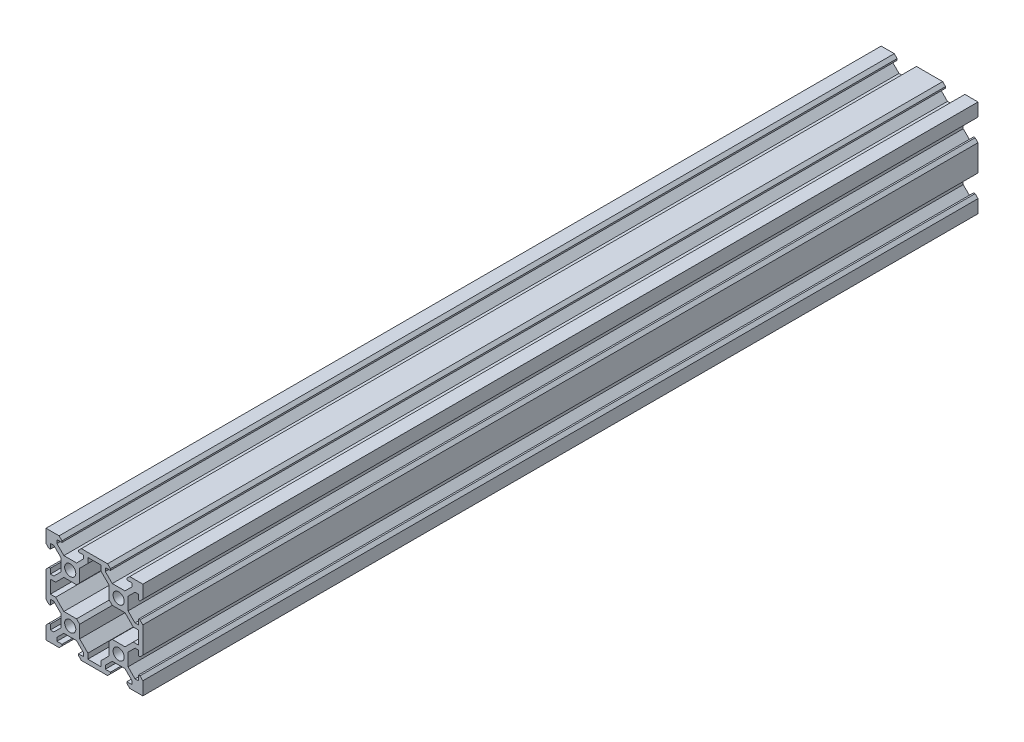
SolidWorks part; units mm, degrees
ref_plane "Front Plane" through (0, 0, 0) normal (0, 0, 1) x (1, 0, 0)
ref_plane "Top Plane" through (0, 0, 0) normal (0, 1, 0) x (1, 0, 0)
ref_plane "Right Plane" through (0, 0, 0) normal (1, 0, 0) x (0, 0, -1)
sketch "Sketch1" plane through (0, 0, 0) normal (0, 0, 1) x (1, 0, 0)
  line L1 (0, 0) -> (40, 0)
  line L2 (0, 0) -> (0, 40)
  line L3 (0, 40) -> (40, 40)
  line L4 (40, 0) -> (40, 40)
  dimension "D1" = 40
extrude "Boss-Extrude1" add sketch "Sketch1" against normal blind 345
sketch "Sketch2" plane through (0, 0, 0) normal (0, 0, 1) x (1, 0, 0)
  line L0 (0, 20) -> (40, 20) construction
  line L1 (0, 40) -> (0, 0) construction
  line L2 (40, 0) -> (40, 40) construction
  line L3 (20, 40) -> (20, 0) construction
  line L4 (40, 40) -> (0, 40) construction
  line L5 (0, 0) -> (40, 0) construction
  line L6 (6.605, 38.815) -> (6.605, 38.2)
  line L7 (6.605, 38.2) -> (4.5, 38.2)
  line L8 (4.5, 38.2) -> (4.5, 36.7728)
  line L9 (4.5, 36.7728) -> (7.3728, 33.9)
  line L10 (7.3728, 33.9) -> (12.6272, 33.9)
  line L11 (12.6272, 33.9) -> (15.5, 36.7728)
  line L12 (15.5, 36.7728) -> (15.5, 38.2)
  line L13 (15.5, 38.2) -> (13.395, 38.2)
  line L14 (13.395, 38.2) -> (13.395, 38.815)
  line L16 (6.605, 38.815) -> (5.42, 40)
  line L17 (13.395, 38.815) -> (14.58, 40)
  line L18 (14.58, 40) -> (5.42, 40)
  line L19 (26.605, 38.815) -> (25.42, 40)
  line L20 (26.605, 38.2) -> (26.605, 38.815)
  line L21 (24.5, 38.2) -> (26.605, 38.2)
  line L22 (24.5, 36.7728) -> (24.5, 38.2)
  line L23 (27.3728, 33.9) -> (24.5, 36.7728)
  line L24 (32.6272, 33.9) -> (27.3728, 33.9)
  line L25 (35.5, 36.7728) -> (32.6272, 33.9)
  line L26 (35.5, 38.2) -> (35.5, 36.7728)
  line L27 (33.395, 38.2) -> (35.5, 38.2)
  line L28 (33.395, 38.815) -> (33.395, 38.2)
  line L29 (33.395, 38.815) -> (34.58, 40)
  line L30 (25.42, 40) -> (34.58, 40)
  line L31 (26.605, 1.8) -> (26.605, 1.185)
  line L32 (24.5, 1.8) -> (26.605, 1.8)
  line L33 (24.5, 3.2272) -> (24.5, 1.8)
  line L34 (27.3728, 6.1) -> (24.5, 3.2272)
  line L35 (32.6272, 6.1) -> (27.3728, 6.1)
  line L36 (35.5, 3.2272) -> (32.6272, 6.1)
  line L37 (35.5, 1.8) -> (35.5, 3.2272)
  line L38 (33.395, 1.8) -> (35.5, 1.8)
  line L39 (33.395, 1.185) -> (33.395, 1.8)
  line L40 (33.395, 1.185) -> (34.58, 0)
  line L41 (25.42, 0) -> (34.58, 0)
  line L42 (26.605, 1.185) -> (25.42, 0)
  line L43 (13.395, 1.185) -> (14.58, 0)
  line L44 (13.395, 1.8) -> (13.395, 1.185)
  line L45 (15.5, 1.8) -> (13.395, 1.8)
  line L46 (15.5, 3.2272) -> (15.5, 1.8)
  line L47 (12.6272, 6.1) -> (15.5, 3.2272)
  line L48 (7.3728, 6.1) -> (12.6272, 6.1)
  line L49 (4.5, 3.2272) -> (7.3728, 6.1)
  line L50 (4.5, 1.8) -> (4.5, 3.2272)
  line L51 (6.605, 1.8) -> (4.5, 1.8)
  line L52 (6.605, 1.185) -> (6.605, 1.8)
  line L53 (6.605, 1.185) -> (5.42, 0)
  line L54 (14.58, 0) -> (5.42, 0)
  line L55 (0, 0) -> (40, 40) construction
  line L56 (1.8, 13.395) -> (1.185, 13.395)
  line L57 (1.8, 15.5) -> (1.8, 13.395)
  line L58 (3.2272, 15.5) -> (1.8, 15.5)
  line L59 (6.1, 12.6272) -> (3.2272, 15.5)
  line L60 (6.1, 7.3728) -> (6.1, 12.6272)
  line L61 (3.2272, 4.5) -> (6.1, 7.3728)
  line L62 (1.8, 4.5) -> (3.2272, 4.5)
  line L63 (1.8, 6.605) -> (1.8, 4.5)
  line L64 (1.185, 6.605) -> (1.8, 6.605)
  line L65 (1.185, 6.605) -> (0, 5.42)
  line L66 (0, 14.58) -> (0, 5.42)
  line L67 (1.185, 13.395) -> (0, 14.58)
  line L68 (0, 40) -> (40, 0) construction
  line L69 (1.185, 26.605) -> (0, 25.42)
  line L70 (1.8, 26.605) -> (1.185, 26.605)
  line L71 (1.8, 24.5) -> (1.8, 26.605)
  line L72 (3.2272, 24.5) -> (1.8, 24.5)
  line L73 (6.1, 27.3728) -> (3.2272, 24.5)
  line L74 (6.1, 32.6272) -> (6.1, 27.3728)
  line L75 (3.2272, 35.5) -> (6.1, 32.6272)
  line L76 (1.8, 35.5) -> (3.2272, 35.5)
  line L77 (1.8, 33.395) -> (1.8, 35.5)
  line L78 (1.185, 33.395) -> (1.8, 33.395)
  line L79 (1.185, 33.395) -> (0, 34.58)
  line L80 (0, 25.42) -> (0, 34.58)
  line L81 (38.2, 15.5) -> (38.2, 13.395)
  line L82 (36.7728, 15.5) -> (38.2, 15.5)
  line L83 (33.9, 12.6272) -> (36.7728, 15.5)
  line L84 (33.9, 7.3728) -> (33.9, 12.6272)
  line L85 (36.7728, 4.5) -> (33.9, 7.3728)
  line L86 (38.2, 4.5) -> (36.7728, 4.5)
  line L87 (38.2, 6.605) -> (38.2, 4.5)
  line L88 (38.815, 6.605) -> (38.2, 6.605)
  line L89 (38.815, 6.605) -> (40, 5.42)
  line L90 (40, 14.58) -> (40, 5.42)
  line L91 (38.815, 13.395) -> (40, 14.58)
  line L92 (38.2, 13.395) -> (38.815, 13.395)
  line L93 (38.2, 26.605) -> (38.815, 26.605)
  line L94 (38.2, 24.5) -> (38.2, 26.605)
  line L95 (36.7728, 24.5) -> (38.2, 24.5)
  line L96 (33.9, 27.3728) -> (36.7728, 24.5)
  line L97 (33.9, 32.6272) -> (33.9, 27.3728)
  line L98 (36.7728, 35.5) -> (33.9, 32.6272)
  line L99 (38.2, 35.5) -> (36.7728, 35.5)
  line L100 (38.2, 33.395) -> (38.2, 35.5)
  line L101 (38.815, 33.395) -> (38.2, 33.395)
  line L102 (38.815, 33.395) -> (40, 34.58)
  line L103 (40, 25.42) -> (40, 34.58)
  line L104 (38.815, 26.605) -> (40, 25.42)
  circle A0 centre (10, 30) radius 2.3
  circle A2 centre (30, 30) radius 2.3
  circle A3 centre (30, 10) radius 2.3
  circle A4 centre (10, 10) radius 2.3
  point P22 (10, 40)
  point P33 (10, 33.9)
  dimension "D1" = 4.6
  dimension "D2" = 20
  dimension "D3" = 20
  dimension "D4" = 4.3
  dimension "D5" = 6.79
  dimension "D6" = 9.16
  dimension "D7" = 11
  dimension "D8" = 90
  dimension "D9" = 1.8
  dimension "D10" = 1.8
extrude "Cut-Extrude1" cut sketch "Sketch2" against normal up to surface (345 mm away) up to face at (20, 20, -345)
sketch "Sketch3" plane through (0, 0, 0) normal (0, 0, 1) x (1, 0, 0)
  line L0 (17.3, 38.2) -> (22.7, 38.2)
  line L1 (0, 20) -> (40, 20) construction
  line L2 (0, 25.42) -> (0, 14.58) construction
  line L3 (40, 14.58) -> (40, 25.42) construction
  line L4 (1.8, 22.7) -> (1.8, 17.3)
  line L5 (12.6272, 13.9) -> (13.9, 12.6272)
  line L6 (13.9, 12.6272) -> (13.9, 7.3728)
  line L7 (7.3728, 13.9) -> (12.6272, 13.9)
  line L8 (13.9, 7.3728) -> (17.3, 3.9728)
  line L9 (17.3, 3.9728) -> (17.3, 1.8)
  line L10 (1.8, 17.3) -> (3.9728, 17.3)
  line L11 (3.9728, 17.3) -> (7.3728, 13.9)
  line L12 (17.3, 1.8) -> (22.7, 1.8)
  line L13 (27.3728, 26.1) -> (26.1, 27.3728)
  line L14 (26.1, 27.3728) -> (26.1, 32.6272)
  line L15 (32.6272, 26.1) -> (27.3728, 26.1)
  line L16 (26.1, 32.6272) -> (22.7, 36.0272)
  line L17 (22.7, 36.0272) -> (22.7, 38.2)
  line L18 (38.2, 22.7) -> (36.0272, 22.7)
  line L19 (36.0272, 22.7) -> (32.6272, 26.1)
  line L20 (36.0272, 17.3) -> (32.6272, 13.9)
  line L21 (38.2, 17.3) -> (36.0272, 17.3)
  line L22 (22.7, 3.9728) -> (22.7, 1.8)
  line L23 (26.1, 7.3728) -> (22.7, 3.9728)
  line L24 (32.6272, 13.9) -> (27.3728, 13.9)
  line L25 (26.1, 12.6272) -> (26.1, 7.3728)
  line L26 (27.3728, 13.9) -> (26.1, 12.6272)
  line L27 (38.2, 22.7) -> (38.2, 17.3)
  line L117 (3.9728, 22.7) -> (7.3728, 26.1)
  line L118 (1.8, 22.7) -> (3.9728, 22.7)
  line L119 (3.9728, 22.7) -> (7.3728, 26.1)
  line L120 (1.8, 22.7) -> (3.9728, 22.7)
  line L134 (20, 40) -> (20, 0) construction
  line L135 (25.42, 40) -> (14.58, 40) construction
  line L136 (17.3, 36.0272) -> (17.3, 38.2)
  line L137 (13.9, 32.6272) -> (17.3, 36.0272)
  line L138 (17.3, 36.0272) -> (17.3, 38.2)
  line L139 (13.9, 32.6272) -> (17.3, 36.0272)
  line L140 (14.58, 0) -> (25.42, 0) construction
  line L141 (7.3728, 26.1) -> (12.6272, 26.1)
  line L142 (13.9, 27.3728) -> (13.9, 32.6272)
  line L155 (12.6272, 26.1) -> (13.9, 27.3728)
  circle A2 centre (10, 30) radius 2.3 construction
  circle A3 centre (10, 30) radius 2.3 construction
  circle A4 centre (10, 10) radius 2.3 construction
  circle A5 centre (30, 10) radius 2.3 construction
  circle A6 centre (30, 30) radius 2.3 construction
  point P24 (10, 26.1)
  point P25 (38.2, 20)
  point P38 (1.8, 20)
  point P52 (20, 1.8)
  point P59 (20, 38.2)
  dimension "D5" = 135
  dimension "D1" = 1.8
  dimension "D3" = 1.8
extrude "Cut-Extrude2" cut sketch "Sketch3" against normal up to surface (345 mm away) up to face at (20, 20, -345)
